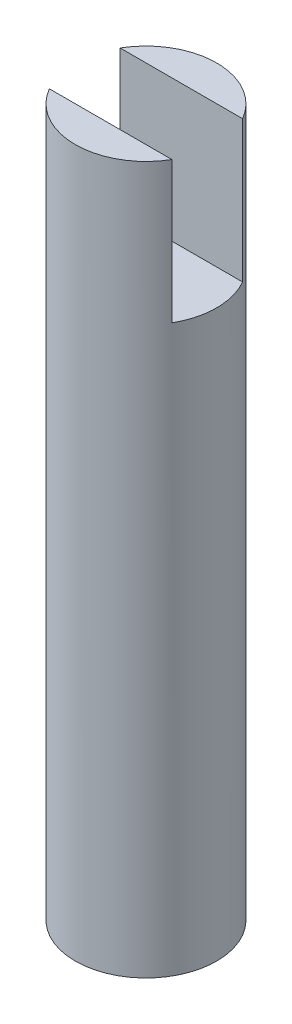
SolidWorks part; units mm, degrees
ref_plane "Front Plane" through (0, 0, 0) normal (0, 0, 1) x (1, 0, 0)
ref_plane "Top Plane" through (0, 0, 0) normal (0, 1, 0) x (1, 0, 0)
ref_plane "Right Plane" through (0, 0, 0) normal (1, 0, 0) x (0, 0, -1)
sketch "Sketch1" plane through (0, 0, 0) normal (0, 1, 0) x (1, 0, 0)
  circle A0 centre (0, 0) radius 5
  dimension "D1" = 10
extrude "Boss-Extrude1" add sketch "Sketch1" along normal blind 5 and the other way blind 45
sketch "Sketch2" plane through (0, 0, 0) normal (1, 0, 0) x (0, 0, -1)
  line L0 (5, 5) -> (-5, 5) construction
  line L1 (-2.5, 5) -> (2.5, 5)
  line L2 (-2.5, 5) -> (-2.5, -5)
  line L3 (-2.5, -5) -> (2.5, -5)
  line L4 (2.5, 5) -> (2.5, -5)
  point P6 (15.5769, 5)
  point P7 (0, 5)
  dimension "D1" = 5
  dimension "D2" = 10
extrude "Cut-Extrude1" cut sketch "Sketch2" against normal through all both and the other way through all
